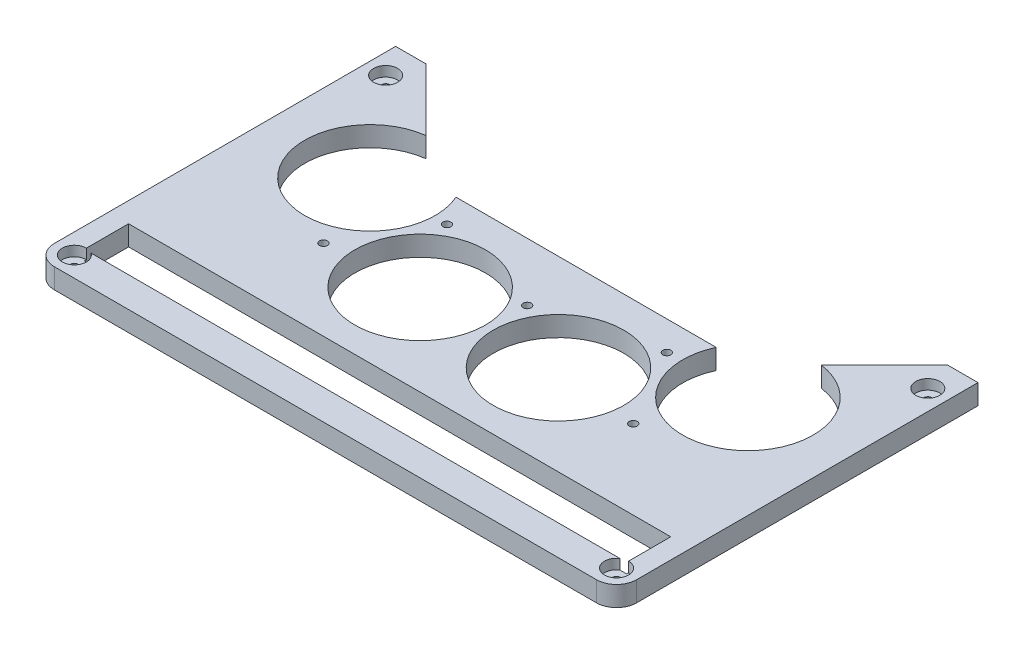
SolidWorks part; units mm, degrees
material "Acrylique (impact moyen-haut)"
ref_plane "Plan de face" through (0, 0, 0) normal (0, 0, 1) x (1, 0, 0)
ref_plane "Plan de dessus" through (0, 0, 0) normal (0, 1, 0) x (1, 0, 0)
ref_plane "Plan de droite" through (0, 0, 0) normal (1, 0, 0) x (0, 0, -1)
sketch "Esquisse2" plane through (0, 0, 0) normal (0, 1, 0) x (1, 0, 0)
  line L0 (145, 290) -> (145, 0) construction
  line L1 (0, 0) -> (290, 0)
  line L2 (0, 0) -> (0, 180)
  line L4 (290, 0) -> (290, 180)
  line L6 (0, 180) -> (15, 180)
  line L7 (15, 180) -> (65, 130)
  line L8 (65, 130) -> (225, 130)
  line L9 (290, 180) -> (275, 180)
  line L10 (275, 180) -> (225, 130)
  point P16 (145, 130)
  dimension "D2" = 290
  dimension "D3" = 15
  dimension "D4" = 50
  dimension "D5" = 130
  dimension "D6" = 135
extrude "Boss.-Extru.1" add sketch "Esquisse2" along normal blind 10
sketch "Esquisse3" plane through (0, 10, 0) normal (0, 1, 0) x (1, 0, 0)
  line L0 (0, 90) -> (290, 90) construction
  line L1 (0, 180) -> (0, 0) construction
  line L2 (290, 0) -> (290, 180) construction
  line L3 (145, 290) -> (145, 0) construction
  line L5 (0, 0) -> (290, 0) construction
  line L6 (0, 180) -> (0, 0) construction
  circle A0 centre (10, 10) radius 2
  circle A1 centre (280, 10) radius 2
  dimension "D3" = 10
  dimension "D1" = 4
  dimension "D2" = 10
extrude "Enlèv. mat.-Extru.1" cut sketch "Esquisse3" against normal blind 10
fillet "Congé1" radius 10 2 edges at (0, 5, 0) (290, 5, 0)
sketch "Esquisse4" plane through (0, 0, 0) normal (0, -1, 0) x (1, 0, 0)
  circle A0 centre (239.1063, -116.3097) radius 32.5
  circle A1 centre (179.1533, -81.9426) radius 32.5
  circle A2 centre (110.0489, -82.1564) radius 32.5
  circle A3 centre (50.3097, -116.8937) radius 32.5
  dimension "D1" = 65
extrude "Enlèv. mat.-Extru.2" cut sketch "Esquisse4" against normal blind 10
sketch "Esquisse5" plane through (0, 0, 0) normal (0, -1, 0) x (-1, 0, 0)
  circle A0 centre (-144.5057, 101.0011) radius 2
  circle A1 centre (-199.5714, 115.491) radius 2
  circle A2 centre (-221.896, 76.4192) radius 2
  circle A3 centre (-66.8976, 77.1157) radius 2
  circle A4 centre (-89.5725, 115.9853) radius 2
extrude "Enlèv. mat.-Extru.3" cut sketch "Esquisse5" against normal blind 10
sketch "Esquisse6" plane through (0, 10, 0) normal (0, 1, 0) x (1, 0, 0)
  line L0 (145, 15) -> (145, 0) construction
  line L1 (10, 37) -> (280, 37)
  line L2 (10, 37) -> (10, 15)
  line L3 (10, 15) -> (280, 15)
  line L4 (280, 37) -> (280, 15)
  line L5 (10, 0) -> (280, 0) construction
  circle A0 centre (280, 10) radius 2 construction
  dimension "D3" = 5
  dimension "D1" = 22
  dimension "D2" = 270
extrude "Enlèv. mat.-Extru.4" cut sketch "Esquisse6" against normal blind 10
sketch "Esquisse7" plane through (0, 10, 0) normal (0, 1, 0) x (1, 0, 0)
  line L0 (145, 0) -> (145, 196.8159) construction
  line L1 (10, 0) -> (280, 0) construction
  line L2 (15, 180) -> (0, 180) construction
  line L3 (0, 180) -> (0, 10) construction
  circle A0 centre (10, 165) radius 2
  circle A1 centre (280, 165) radius 2
  dimension "D1" = 4
  dimension "D3" = 10
  dimension "D2" = 15
extrude "Enlèv. mat.-Extru.5" cut sketch "Esquisse7" against normal blind 10
ref_plane "Plan1" through (0, 5, 0) normal (0, 1, 0) x (1, 0, 0)
sketch "Esquisse10" plane through (0, 10, 0) normal (0, 1, 0) x (1, 0, 0)
  circle A0 centre (10, 165) radius 6
  circle A1 centre (280, 165) radius 6
  circle A2 centre (280, 10) radius 6
  circle A3 centre (10, 10) radius 6
  dimension "D1" = 12
extrude "Enlèv. mat.-Extru.6" cut sketch "Esquisse10" against normal blind 5
